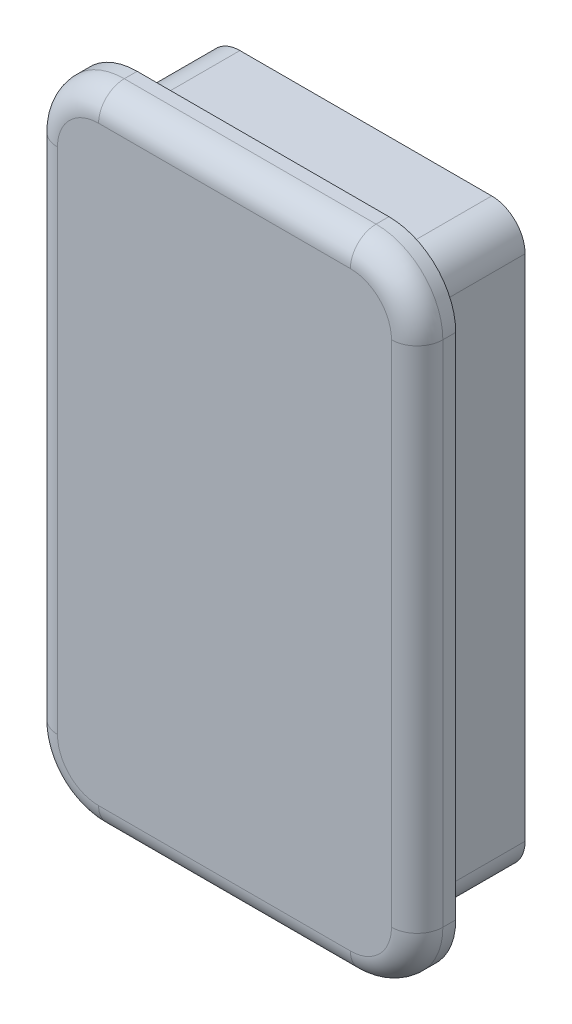
SolidWorks part; units mm, degrees
material "Nylon 101"
ref_plane "Front Plane" through (0, 0, 0) normal (0, 0, 1) x (1, 0, 0)
ref_plane "Top Plane" through (0, 0, 0) normal (0, 1, 0) x (1, 0, 0)
ref_plane "Right Plane" through (0, 0, 0) normal (1, 0, 0) x (0, 0, -1)
sketch "Sketch1" plane through (0, 0, 0) normal (0, 0, 1) x (1, 0, 0)
  line L0 (-9.8, -22.4) -> (9.8, -22.4)
  line L1 (-12.4, -19.8) -> (-12.4, 19.8)
  line L2 (9.8, 22.4) -> (-9.8, 22.4)
  line L3 (12.4, 19.8) -> (12.4, -19.8)
  line L4 (-9.8, -25) -> (9.8, -25)
  line L5 (-15, -19.8) -> (-15, 19.8)
  line L6 (9.8, 25) -> (-9.8, 25)
  line L7 (15, 19.8) -> (15, -19.8)
  arc A0 (15, 19.8) -> (9.8, 25) centre (9.8, 19.8) ccw
  arc A1 (9.8, -25) -> (15, -19.8) centre (9.8, -19.8) ccw
  arc A2 (-15, -19.8) -> (-9.8, -25) centre (-9.8, -19.8) ccw
  arc A3 (-9.8, 25) -> (-15, 19.8) centre (-9.8, 19.8) ccw
  arc A4 (-9.8, 22.4) -> (-12.4, 19.8) centre (-9.8, 19.8) ccw
  arc A5 (12.4, 19.8) -> (9.8, 22.4) centre (9.8, 19.8) ccw
  arc A6 (9.8, -22.4) -> (12.4, -19.8) centre (9.8, -19.8) ccw
  arc A7 (-12.4, -19.8) -> (-9.8, -22.4) centre (-9.8, -19.8) ccw
  point P0 (0, 25)
  point P1 (15, 0)
  point P2 (0, -25)
  point P3 (-15, 0)
  point P4 (-15, 25)
  point P5 (15, 25)
  point P6 (15, -25)
  point P7 (-15, -25)
  point P8 (0, 0)
  point P33 (0, 0)
  dimension "D1" = 5.2
  dimension "Thickness" = 2.6
  dimension "V_leg" = 50
  dimension "H_leg" = 30
extrude "Boss-Extrude1" add sketch "Sketch1" against normal blind 8 contours L2 A4 L1 A7 L0 A6 L3 A5
sketch "Sketch3" plane through (0, 0, 0) normal (0, 0, 1) x (1, 0, 0)
  line L4 (-9.8, -25) -> (9.8, -25)
  line L5 (-15, -19.8) -> (-15, 19.8)
  line L6 (9.8, 25) -> (-9.8, 25)
  line L7 (15, 19.8) -> (15, -19.8)
  line L8 (-15, 0) -> (15, 0) construction
  arc A0 (15, 19.8) -> (9.8, 25) centre (9.8, 19.8) ccw
  arc A1 (9.8, -25) -> (15, -19.8) centre (9.8, -19.8) ccw
  arc A2 (-15, -19.8) -> (-9.8, -25) centre (-9.8, -19.8) ccw
  arc A3 (-9.8, 25) -> (-15, 19.8) centre (-9.8, 19.8) ccw
  point P0 (0, 25)
  point P1 (15, 0)
  point P2 (0, -25)
  point P3 (-15, 0)
  point P6 (0, 0)
  dimension "D1" = 5.2
  dimension "V_leg" = 50
  dimension "H_leg" = 30
extrude "Boss-Extrude3" add sketch "Sketch3" along normal blind 3
fillet "Fillet1" radius 2 8 edges at (13.477, -23.477, 3) (0, -25, 3) (-13.477, -23.477, 3) (-15, 0, 3) (-13.477, 23.477, 3) (0, 25, 3) (13.477, 23.477, 3) (15, 0, 3)
shell "Shell1" thickness 2
